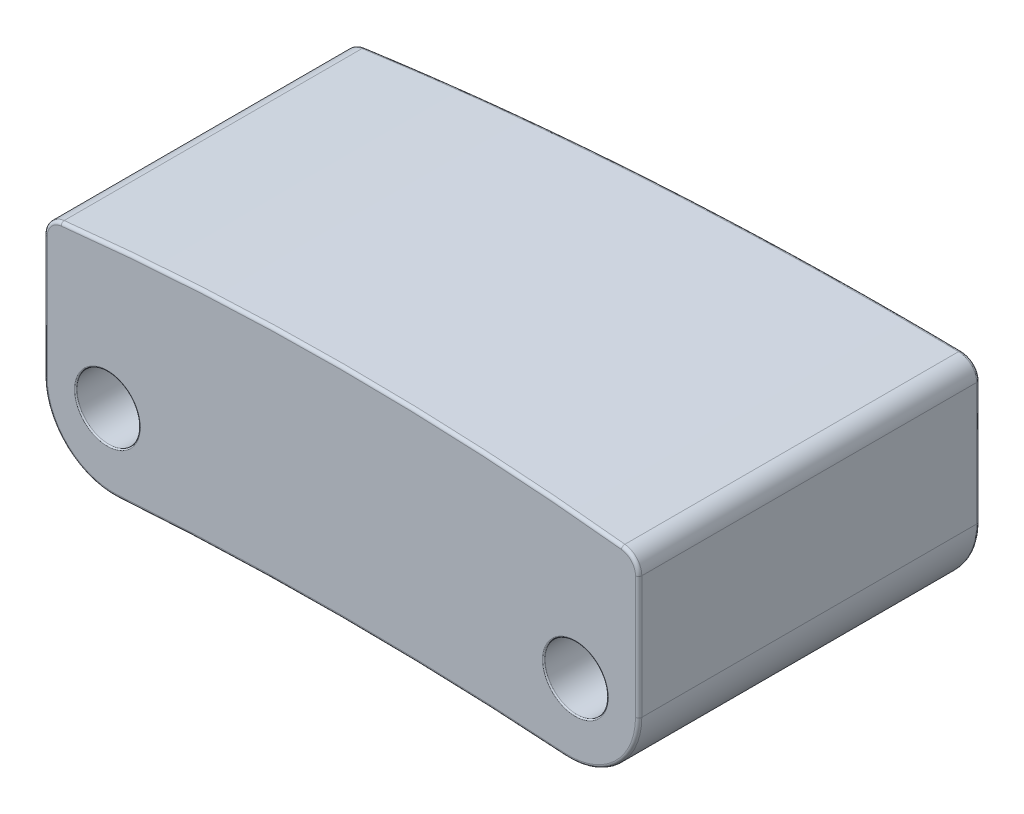
SolidWorks part; units mm, degrees
ref_plane "Front Plane" through (0, 0, 0) normal (0, 0, 1) x (1, 0, 0)
ref_plane "Top Plane" through (0, 0, 0) normal (0, 1, 0) x (1, 0, 0)
ref_plane "Right Plane" through (0, 0, 0) normal (1, 0, 0) x (0, 0, -1)
sketch "Sketch1" plane through (0, 0, 0) normal (0, 0, 1) x (1, 0, 0)
  line L0 (55, 0) -> (-55, 0) construction
  line L1 (-4.7, 1.85) -> (4.7, 1.85)
  line L2 (-4.7, 1.85) -> (-4.7, -1.85)
  line L3 (-4.7, -1.85) -> (4.7, -1.85)
  line L4 (4.7, 1.85) -> (4.7, -1.85)
  line L5 (0, -55) -> (0, 55) construction
  dimension "D1" = 9.4
  dimension "D2" = 3.7
  dimension "D3" = 1.85
  dimension "D4" = 4.7
extrude "Boss-Extrude1" add sketch "Sketch1" along normal mid plane 5.4
sketch "Sketch2" plane through (0, 0, 2.7) normal (0, 0, 1) x (1, 0, 0)
  line L0 (-4.7, 1.85) -> (-4.7, -1.85) construction
  line L1 (4.7, -1.85) -> (4.7, 1.85) construction
  line L2 (-4.7, -1.85) -> (4.7, -1.85) construction
  line L3 (4.7, 1.85) -> (-4.7, 1.85) construction
  line L4 (-4.7, 1.55) -> (-7.1207, 4.0114)
  line L5 (-7.1207, 4.0114) -> (5.5359, 3.8867)
  line L6 (5.5359, 3.8867) -> (4.7, 1.55)
  line L7 (4.7, -1.85) -> (0.3506, -3.782)
  line L8 (-4.7, -1.85) -> (0.3506, -3.782)
  arc A0 (-4.7, 1.55) -> (4.7, 1.55) centre (0, -38.1729) cw
  arc A1 (-4.7, -1.85) -> (4.7, -1.85) centre (0, -51.6286) cw
  dimension "D4" = 40
  dimension "D5" = 50
  dimension "D1" = 0
  dimension "D2" = 0.3
  dimension "D3" = 0.3
extrude "Cut-Extrude1" cut sketch "Sketch2" against normal blind 15.2
fillet "Fillet1" radius 1.1 2 edges at (4.7, -1.85, 0) (-4.7, -1.85, 0)
fillet "Fillet2" radius 0.3 2 edges at (4.7, 1.55, 0) (-4.7, 1.55, 0)
sketch "Sketch3" plane through (0, 0, 2.7) normal (0, 0, 1) x (1, 0, 0)
  line L0 (2.97, 0) -> (-2.97, 0) construction
  line L1 (0, -1.9705) -> (0, 1.9705) construction
  circle A0 centre (3.7, -0.6) radius 0.5
  circle A1 centre (-3.7, -0.6) radius 0.5
  dimension "D1" = 1
  dimension "D2" = 0.6
  dimension "D3" = 0.6
  dimension "D4" = 1
  dimension "D5" = 3.7
  dimension "D6" = 3.7
extrude "Cut-Extrude2" cut sketch "Sketch3" against normal blind 3
fillet "Fillet4" radius 0.02 2 edges at (4.2, -0.6, 2.7) (-3.2, -0.6, 2.7)
sketch "Sketch4" plane through (0, 0, 0) normal (0, 1, 0) x (1, 0, 0)
  line L0 (-4.4332, -2.7) -> (4.4332, -2.7) construction
  line L1 (4.7, 2.7) -> (4.7, -2.7) construction
  line L2 (-4.7, -2.7) -> (-4.7, 2.7) construction
  line L4 (-4.7, 2.1) -> (-6.6127, 3.6139)
  line L5 (-6.6127, 3.6139) -> (6.4207, 4.4741)
  line L6 (6.4207, 4.4741) -> (4.7, 2.7)
  arc A0 (4.7, 2.7) -> (-4.7, 2.1) centre (-9.5503, 152.0216) cw
  dimension "D5" = 150
  dimension "D1" = 0
  dimension "D2" = 0
  dimension "D3" = 4.8
  dimension "D4" = 5.4
extrude "Cut-Extrude3" cut sketch "Sketch4" against normal mid plane 10
fillet "Fillet5" radius 0.05 17 edges at (4.7, 0.3135, 2.7) (4.3499, -1.4603, 2.7) (0, -1.6286, 2.7) (-4.7, 0.3135, -2.1) (4.6127, 1.494, -2.6917) (-4.2253, -1.5605, -2.1161) (4.4608, -1.3404, -2.6774) (4.2, -0.6, -0.3) (0, 1.8271, 2.7) (4.7, 0.3135, -2.7) (-4.7, 0.3135, 2.7) (-4.3499, -1.4603, 2.7) (-4.6236, 1.4825, 2.7) (4.6236, 1.4825, 2.7) (-4.6343, 1.4698, -2.1021)
sketch "Sketch5" plane through (0, 0, 0) normal (0, 1, 0) x (1, 0, 0)
  line L0 (-4.7, 2.0516) -> (-4.7, -2.65) construction
  line L1 (-3.526, -2.7) -> (3.526, -2.7) construction
  circle A0 centre (-0.7, -1.2) radius 0.4
  dimension "D1" = 4
  dimension "D2" = 1.5
  dimension "D3" = 0.8
extrude "Cut-Extrude4" cut sketch "Sketch5" along normal offset from surface (8.7665 mm away) 0.4 from offset 10 offset against normal yes
fillet "Fillet6" radius 0.05 1 edges at (-0.792, -1.6349, 1.5893)
